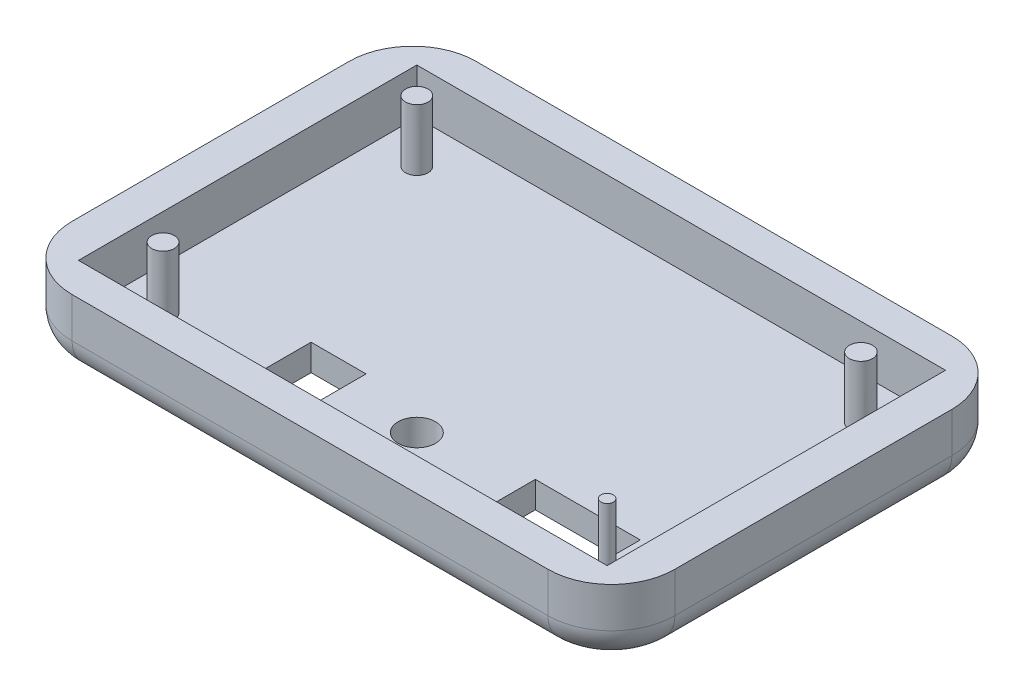
SolidWorks part; units mm, degrees
ref_plane "Front Plane" through (0, 0, 0) normal (0, 0, 1) x (1, 0, 0)
ref_plane "Top Plane" through (0, 0, 0) normal (0, 1, 0) x (1, 0, 0)
ref_plane "Right Plane" through (0, 0, 0) normal (1, 0, 0) x (0, 0, -1)
sketch "Sketch1" plane through (0, 0, 0) normal (0, 1, 0) x (1, 0, 0)
  line L1 (0, 0) -> (72.39, 0)
  line L2 (0, 0) -> (0, 48.514)
  line L3 (0, 48.514) -> (72.39, 48.514)
  line L4 (72.39, 0) -> (72.39, 48.514)
  dimension "D1" = 48.514
  dimension "D2" = 72.39
extrude "Boss-Extrude1" add sketch "Sketch1" along normal blind 8.636
sketch "Sketch2" plane through (0, 8.636, 0) normal (0, 1, 0) x (1, 0, 0)
  line L0 (0, 24.257) -> (72.39, 24.257) construction
  line L1 (0, 48.514) -> (0, 0) construction
  line L2 (72.39, 0) -> (72.39, 48.514) construction
  line L4 (4.445, 3.937) -> (67.945, 3.937)
  line L5 (4.445, 3.937) -> (4.445, 44.577)
  line L6 (4.445, 44.577) -> (67.945, 44.577)
  line L7 (67.945, 3.937) -> (67.945, 44.577)
  line L8 (4.445, 3.937) -> (67.945, 44.577) construction
  line L9 (4.445, 44.577) -> (67.945, 3.937) construction
  point P6 (36.195, 24.257)
  dimension "D1" = 40.64
  dimension "D2" = 63.5
extrude "Cut-Extrude1" cut sketch "Sketch2" against normal blind 5.461
fillet "Fillet2" radius 7.62 4 edges at (72.39, 4.318, -48.514) (72.39, 4.318, 0) (0, 4.318, 0) (0, 4.318, -48.514)
fillet "Fillet3" radius 3.81 8 edges at (70.1582, 0, -46.2822) (72.39, 0, -24.257) (70.1582, 0, -2.2318) (36.195, 0, 0) (2.2318, 0, -2.2318) (0, 0, -24.257) (2.2318, 0, -46.2822) (36.195, 0, -48.514)
sketch "Sketch4" plane through (0, 3.175, 0) normal (0, 1, 0) x (1, 0, 0)
  line L2 (4.445, 44.577) -> (4.445, 3.937) construction
  line L3 (67.945, 3.937) -> (67.945, 44.577) construction
  line L4 (61.799, 14.057) -> (49.199, 14.057)
  line L5 (61.799, 14.057) -> (61.799, 9.057)
  line L6 (61.799, 9.057) -> (49.199, 9.057)
  line L7 (49.199, 14.057) -> (49.199, 9.057)
  line L8 (61.799, 14.057) -> (49.199, 9.057) construction
  line L9 (61.799, 9.057) -> (49.199, 14.057) construction
  line L10 (4.445, 3.937) -> (67.945, 3.937) construction
  line L11 (28.067, 14.859) -> (21.463, 14.859)
  line L12 (28.067, 14.859) -> (28.067, 8.255)
  line L13 (28.067, 8.255) -> (21.463, 8.255)
  line L14 (21.463, 14.859) -> (21.463, 8.255)
  line L15 (28.067, 14.859) -> (21.463, 8.255) construction
  line L16 (28.067, 8.255) -> (21.463, 14.859) construction
  circle A0 centre (37.211, 11.811) radius 2.25
  point P7 (55.499, 11.557)
  point P15 (24.765, 11.557)
  dimension "D3" = 4.5
  dimension "D2" = 32.766
  dimension "D4" = 7.62
  dimension "D5" = 12.6
  dimension "D6" = 5
  dimension "D7" = 12.446
  dimension "D8" = 6.604
  dimension "D9" = 6.604
  dimension "D10" = 7.62
  dimension "D11" = 20.32
  dimension "D12" = 7.874
extrude "Cut-Extrude2" cut sketch "Sketch4" against normal blind 7.366
sketch "Sketch5" plane through (0, 3.175, 0) normal (0, 1, 0) x (1, 0, 0)
  line L0 (4.445, 44.577) -> (4.445, 3.937) construction
  line L2 (67.945, 44.577) -> (4.445, 44.577) construction
  line L3 (4.445, 3.937) -> (67.945, 3.937) construction
  line L4 (67.945, 3.937) -> (67.945, 44.577) construction
  circle A0 centre (9.525, 39.497) radius 1.35
  circle A1 centre (9.525, 9.017) radius 1.35
  circle A2 centre (62.865, 39.497) radius 1.385
  circle A3 centre (62.865, 9.017) radius 0.75
  point P18 (67.056, 8.2679)
  dimension "D5" = 2.7
  dimension "D6" = 2.7
  dimension "D7" = 1.5
  dimension "D8" = 2.77
  dimension "D11" = 5.08
  dimension "D1" = 5.08
  dimension "D2" = 5.08
  dimension "D3" = 5.08
  dimension "D4" = 5.08
  dimension "D9" = 5.08
  dimension "D10" = 5.08
  dimension "D12" = 5.08
extrude "Boss-Extrude2" add sketch "Sketch5" along normal blind 7.366
